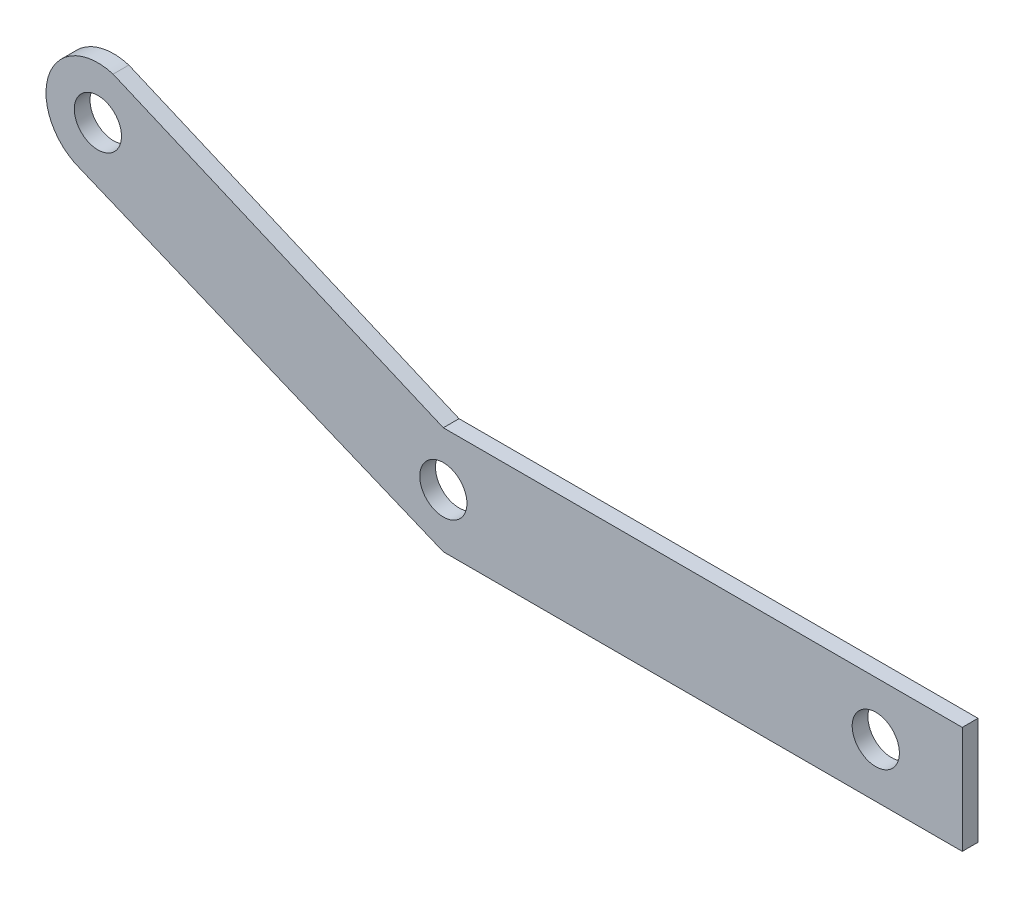
SolidWorks part; units mm, degrees
ref_plane "Alzado" through (0, 0, 0) normal (0, 0, 1) x (1, 0, 0)
ref_plane "Planta" through (0, 0, 0) normal (0, 1, 0) x (1, 0, 0)
ref_plane "Vista lateral" through (0, 0, 0) normal (1, 0, 0) x (0, 0, -1)
sketch "Model" plane through (0, 0, 0) normal (0, 0, 1) x (1, 0, 0)
  line L0 (36.4137, 15.5605) -> (36.4137, 8.7295)
  line L8 (36.4137, 15.5605) -> (3.4137, 15.5605)
  line L9 (3.4137, 15.5605) -> (-17.587, 24.5348)
  line L10 (-19.7197, 18.2925) -> (3.4137, 8.7295)
  line L11 (3.4137, 8.7295) -> (36.4137, 8.7295)
  arc A9 (-17.587, 24.5348) -> (-19.7197, 18.2925) centre (-18.5533, 21.3795) ccw
  circle A23 centre (30.9137, 12.145) radius 1.5
  circle A24 centre (3.4137, 12.145) radius 1.5
  circle A25 centre (-18.5533, 21.3795) radius 1.5
  dimension "D1" = 33
extrude "Saliente-Extruir1" add sketch "Model" along normal blind 1
